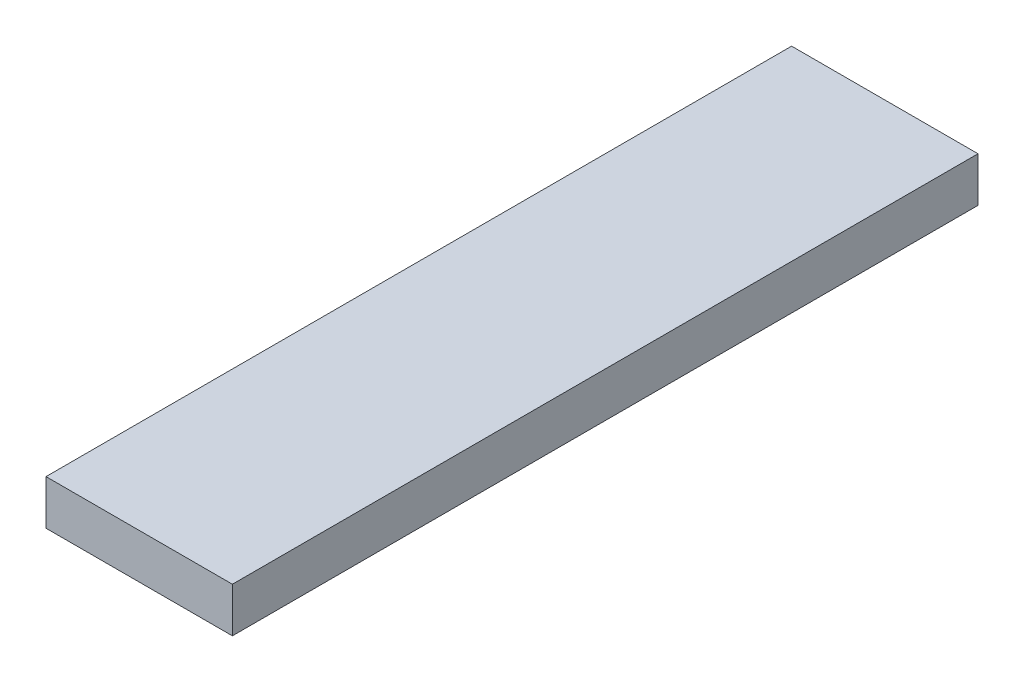
SolidWorks part; units mm, degrees
ref_plane "Front Plane" through (0, 0, 0) normal (0, 0, 1) x (1, 0, 0)
ref_plane "Top Plane" through (0, 0, 0) normal (0, 1, 0) x (1, 0, 0)
ref_plane "Right Plane" through (0, 0, 0) normal (1, 0, 0) x (0, 0, -1)
sketch "Sketch1" plane through (0, 0, 0) normal (1, 0, 0) x (0, 0, -1)
  line L1 (0, 0) -> (40, 0)
  line L2 (0, 0) -> (0, 2.4)
  line L3 (0, 2.4) -> (40, 2.4)
  line L4 (40, 0) -> (40, 2.4)
  dimension "D1" = 40
  dimension "D2" = 2.4
extrude "Boss-Extrude1" add sketch "Sketch1" along normal blind 10
